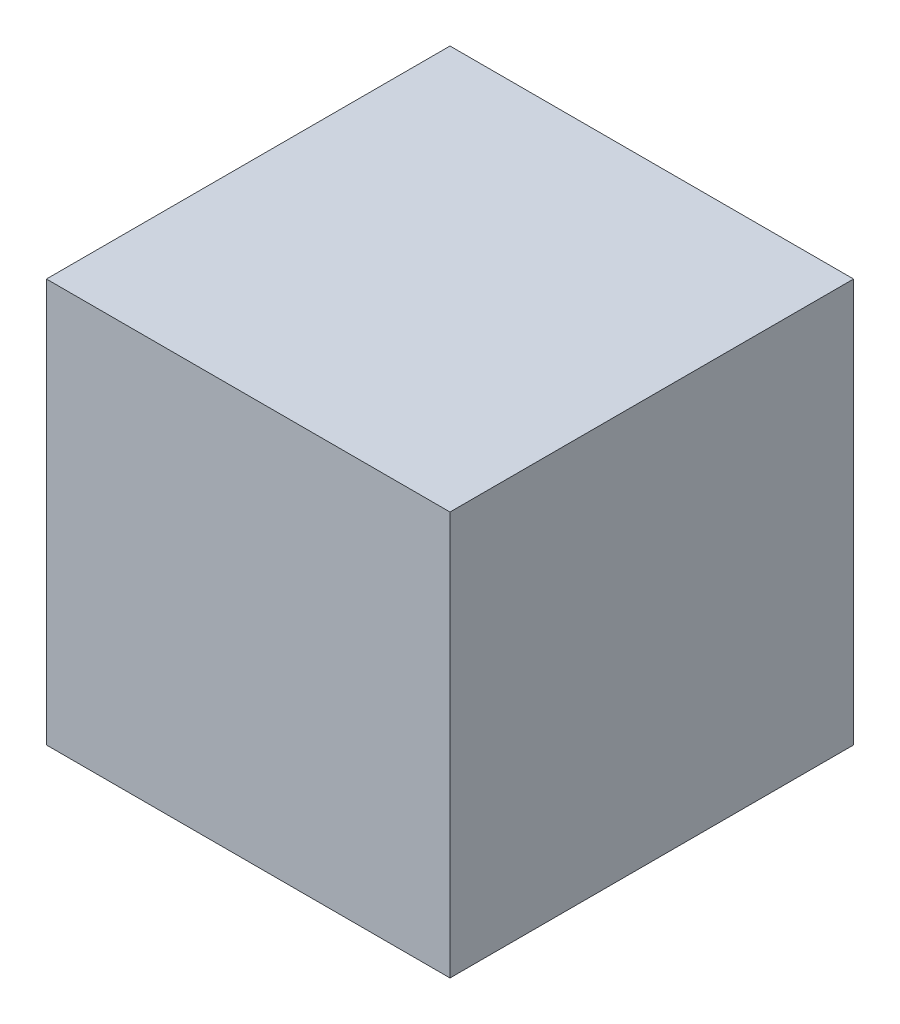
SolidWorks part; units mm, degrees
ref_plane "Front" through (0, 0, 0) normal (0, 0, 1) x (1, 0, 0)
ref_plane "Top" through (0, 0, 0) normal (0, 1, 0) x (1, 0, 0)
ref_plane "Right" through (0, 0, 0) normal (1, 0, 0) x (0, 0, -1)
sketch "Sketch1" plane through (0, 0, 0) normal (0, 1, 0) x (1, 0, 0)
  line L1 (-5, -5) -> (5, -5)
  line L2 (-5, -5) -> (-5, 5)
  line L3 (-5, 5) -> (5, 5)
  line L4 (5, -5) -> (5, 5)
  line L5 (-5, -5) -> (5, 5) construction
  line L6 (-5, 5) -> (5, -5) construction
  point P0 (0, 0)
  dimension "D1" = 10
extrude "Boss-Extrude1" add sketch "Sketch1" along normal blind 10
